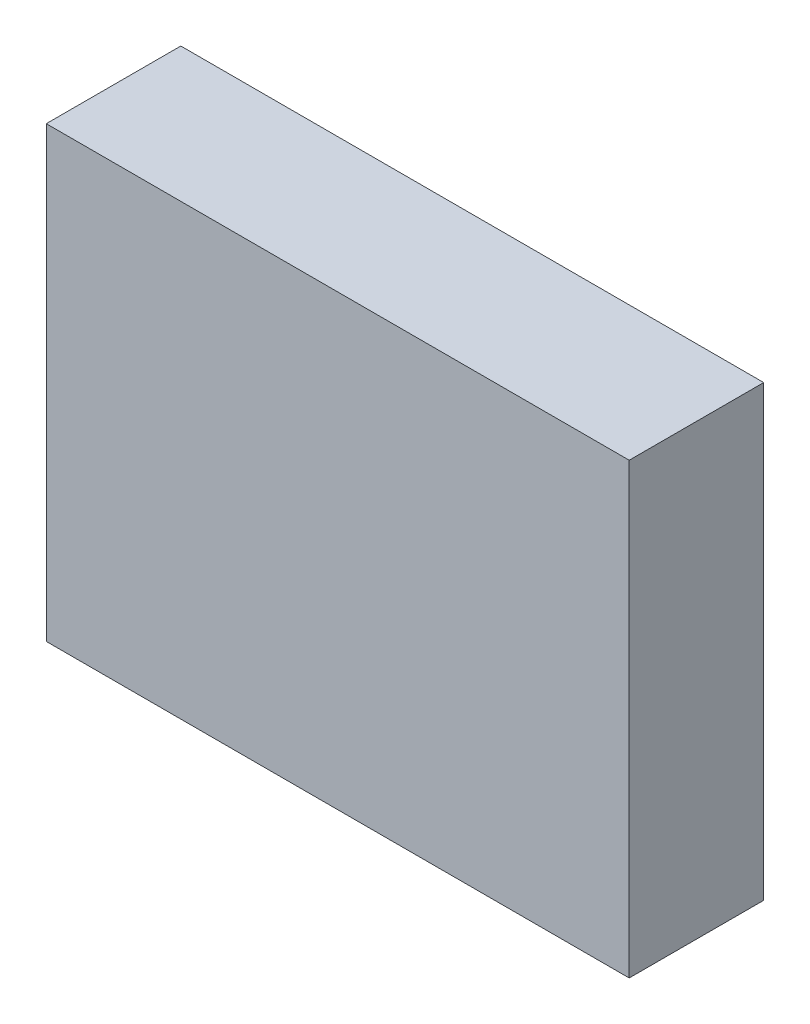
SolidWorks part; units mm, degrees
ref_plane "Front Plane" through (0, 0, 0) normal (0, 0, 1) x (1, 0, 0)
ref_plane "Top Plane" through (0, 0, 0) normal (0, 1, 0) x (1, 0, 0)
ref_plane "Right Plane" through (0, 0, 0) normal (1, 0, 0) x (0, 0, -1)
sketch "Sketch1" plane through (0, 0, 0) normal (0, 0, 1) x (1, 0, 0)
  line L1 (-65, -50) -> (65, -50)
  line L2 (-65, -50) -> (-65, 50)
  line L3 (-65, 50) -> (65, 50)
  line L4 (65, -50) -> (65, 50)
  line L5 (-65, -50) -> (65, 50) construction
  line L6 (-65, 50) -> (65, -50) construction
  point P0 (0, 0)
  dimension "D1" = 100
  dimension "D2" = 130
extrude "Boss-Extrude1" add sketch "Sketch1" along normal blind 30
